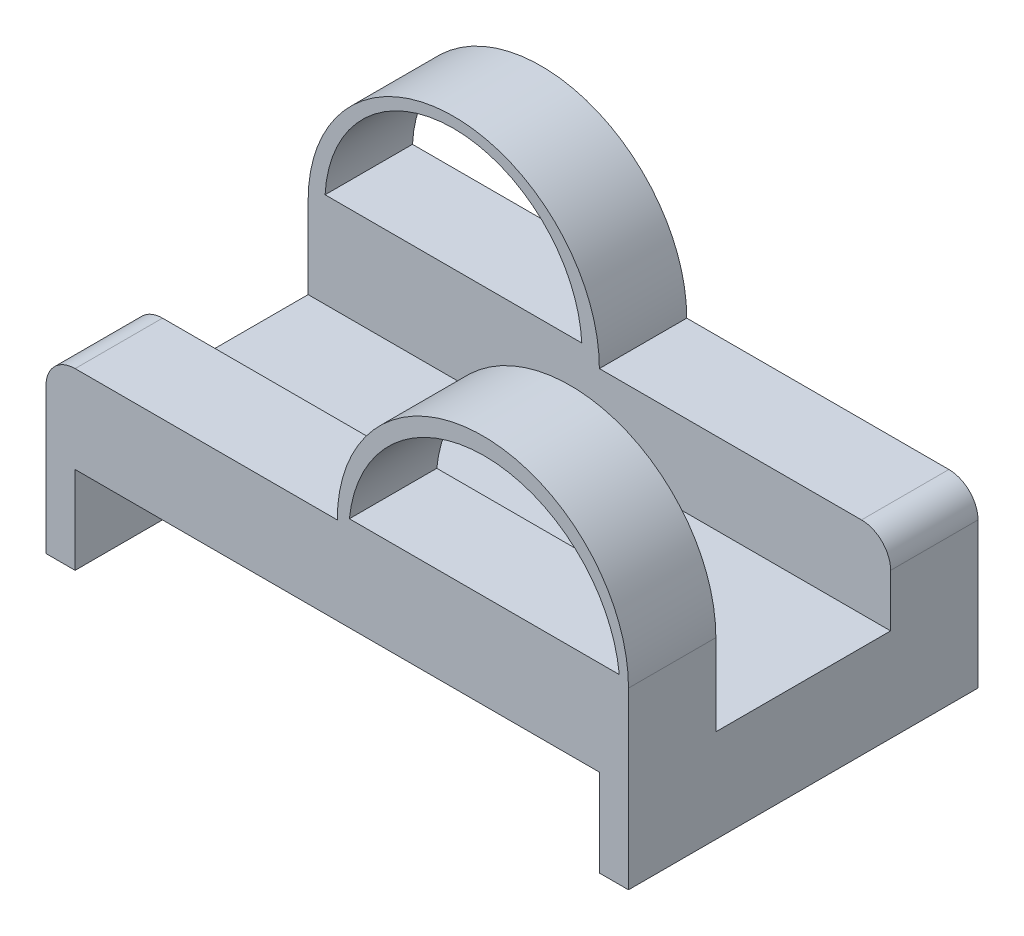
SolidWorks part; units mm, degrees
ref_plane "Front Plane" through (0, 0, 0) normal (0, 0, 1) x (1, 0, 0)
ref_plane "Top Plane" through (0, 0, 0) normal (0, 1, 0) x (1, 0, 0)
ref_plane "Right Plane" through (0, 0, 0) normal (1, 0, 0) x (0, 0, -1)
sketch "Sketch1" plane through (0, 0, 0) normal (0, 0, 1) x (1, 0, 0)
  line L0 (-74.5714, -3.4286) -> (-74.5714, 11.5714)
  line L1 (-74.5714, 11.5714) -> (15.4286, 11.5714)
  line L2 (15.4286, 11.5714) -> (15.4286, -3.4286)
  line L3 (-74.5714, -3.4286) -> (-79.5714, -3.4286)
  line L4 (-79.5714, -3.4286) -> (-79.5714, 26.5714)
  line L5 (-79.5714, 26.5714) -> (20.4286, 26.5714)
  line L6 (20.4286, 26.5714) -> (20.4286, -3.4286)
  line L7 (20.4286, -3.4286) -> (15.4286, -3.4286)
  dimension "D1" = 30
  dimension "D2" = 15
  dimension "D3" = 90
  dimension "D4" = 5
extrude "Boss-Extrude1" add sketch "Sketch1" against normal blind 60
sketch "Sketch3" plane through (0, 0, -60) normal (0, 0, -1) x (-1, 0, 0)
  line L0 (-20.4286, 26.5714) -> (79.5714, 26.5714) construction
  line L1 (29.5714, 26.5714) -> (79.5714, 26.5714)
  arc A0 (79.5714, 26.5714) -> (29.5714, 26.5714) centre (54.5714, 26.5714) ccw
  dimension "D1" = 25
extrude "Boss-Extrude2" add sketch "Sketch3" against normal blind 15
sketch "Sketch4" plane through (0, 0, 0) normal (0, 0, 1) x (1, 0, 0)
  line L0 (20.4286, 26.5714) -> (-79.5714, 26.5714) construction
  line L9 (-79.5714, -3.4286) -> (-74.5714, -3.4286)
  line L10 (-74.5714, -3.4286) -> (-74.5714, 11.5714)
  line L11 (-74.5714, 11.5714) -> (15.4286, 11.5714)
  line L12 (15.4286, 11.5714) -> (15.4286, -3.4286)
  line L13 (15.4286, -3.4286) -> (20.4286, -3.4286)
  line L14 (20.4286, -3.4286) -> (20.4286, 26.5714)
  line L15 (20.4286, 26.5714) -> (-79.5714, 26.5714)
  line L16 (-79.5714, 26.5714) -> (-79.5714, -3.4286)
  line L23 (20.4286, 26.5714) -> (-29.5714, 26.5714)
  arc A0 (20.4286, 26.5714) -> (-29.5714, 26.5714) centre (-4.5714, 26.5714) ccw
  dimension "D1" = 25
  dimension "D2" = 0
extrude "Boss-Extrude4" add sketch "Sketch4" against normal blind 15
sketch "Sketch5" plane through (0, 0, 0) normal (0, 0, 1) x (1, 0, 0)
  line L0 (-27.4867, 27.7877) -> (18.8431, 27.7877)
  arc A0 (18.8431, 27.7877) -> (-27.4867, 27.7877) centre (-4.3218, 25.4463) ccw
extrude "Cut-Extrude3" cut sketch "Sketch5" against normal blind 25
sketch "Sketch6" plane through (0, 0, -45) normal (0, 0, 1) x (1, 0, 0)
  line L0 (-76.6575, 28.8689) -> (-32.592, 28.8689)
  arc A0 (-32.592, 28.8689) -> (-76.6575, 28.8689) centre (-54.6248, 27.7047) ccw
extrude "Cut-Extrude4" cut sketch "Sketch6" against normal blind 25
fillet "Fillet2" radius 5 1 edges at (-79.5714, 26.5714, -22.5)
fillet "Fillet3" radius 5 1 edges at (20.4286, 26.5714, -37.5)
sketch "Sketch10" plane through (0, 26.5714, 0) normal (0, 1, 0) x (1, 0, 0)
  line L1 (-79.5714, 45) -> (20.4286, 45)
  line L2 (-79.5714, 45) -> (-79.5714, 15)
  line L3 (-79.5714, 15) -> (20.4286, 15)
  line L4 (20.4286, 45) -> (20.4286, 15)
extrude "Cut-Extrude8" cut sketch "Sketch10" against normal blind 15
sketch "Sketch12" plane through (0, 11.5714, 0) normal (0, 1, 0) x (1, 0, 0)
  line L1 (-79.5714, 45) -> (20.4286, 45)
  line L2 (-79.5714, 45) -> (-79.5714, 15)
  line L3 (-79.5714, 15) -> (20.4286, 15)
  line L4 (20.4286, 45) -> (20.4286, 15)
extrude "Boss-Extrude10" add sketch "Sketch12" along normal blind 1
